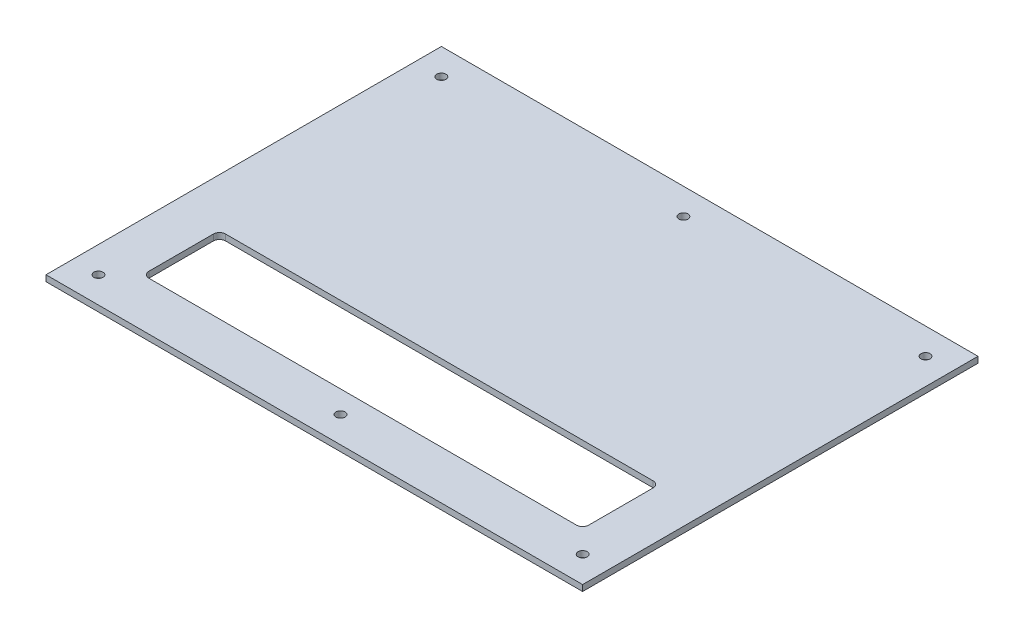
SolidWorks part; units mm, degrees
ref_plane "Спереди" through (0, 0, 0) normal (0, 0, 1) x (1, 0, 0)
ref_plane "Сверху" through (0, 0, 0) normal (0, 1, 0) x (1, 0, 0)
ref_plane "Справа" through (0, 0, 0) normal (1, 0, 0) x (0, 0, -1)
sketch "Эскиз1" plane through (0, 0, 0) normal (0, 1, 0) x (1, 0, 0)
  line L0 (0, 0) -> (266, 0)
  line L1 (0, 0) -> (0, 196)
  line L2 (266, 0) -> (266, 196)
  line L3 (0, 196) -> (266, 196)
  line L4 (13, 183) -> (253, 183) construction
  line L5 (13, 183) -> (13, 13) construction
  line L6 (253, 183) -> (253, 13) construction
  line L7 (13, 13) -> (253, 13) construction
  circle A0 centre (13, 183) radius 2.25
  circle A1 centre (253, 183) radius 2.25
  circle A2 centre (253, 13) radius 2.25
  circle A3 centre (13, 13) radius 2.25
  circle A4 centre (133, 13) radius 2.25
  circle A5 centre (133, 183) radius 2.25
  dimension "D7" = 4.5
  dimension "D8" = 4.5
  dimension "D9" = 4.5
  dimension "D10" = 4.5
  dimension "D11" = 4.5
  dimension "D12" = 4.5
  dimension "D1" = 196
  dimension "D2" = 266
  dimension "D3" = 13
  dimension "D4" = 13
  dimension "D5" = 13
  dimension "D6" = 13
extrude "Бобышка-Вытянуть1" add sketch "Эскиз1" along normal blind 3
sketch "Эскиз2" plane through (0, 3, 0) normal (0, 1, 0) x (1, 0, 0)
  line L0 (3, 193) -> (3, 3) construction
  line L1 (3, 193) -> (263, 193) construction
  line L2 (3, 3) -> (263, 3) construction
  line L3 (263, 193) -> (263, 3) construction
  line L4 (266, 196) -> (0, 196) construction
  line L5 (0, 196) -> (0, 0) construction
  dimension "D1" = 260
  dimension "D2" = 190
  dimension "D3" = 3
  dimension "D4" = 3
sketch "Sketch1" plane through (0, 0, 0) normal (0, -1, 0) x (1, 0, 0)
  line L0 (24, -24) -> (242, -24)
  line L1 (24, -24) -> (24, -62)
  line L2 (242, -24) -> (242, -62)
  line L3 (24, -62) -> (242, -62)
  line L4 (23, -43) -> (23, -62)
  line L5 (243, -43) -> (23, -43)
  line L6 (243, -62) -> (243, -43)
  line L7 (23, -62) -> (243, -62)
  line L8 (23, -43) -> (23, -62) construction
  line L9 (243, -43) -> (23, -43) construction
  line L10 (243, -62) -> (243, -43) construction
  line L11 (23, -62) -> (243, -62) construction
  line L12 (243, -43) -> (243, -23)
  line L13 (243, -23) -> (23, -23)
  line L14 (23, -23) -> (23, -43)
  line L15 (23, -43) -> (243, -43)
  line L16 (243, -43) -> (243, -23) construction
  line L17 (243, -23) -> (23, -23) construction
  line L18 (23, -23) -> (23, -43) construction
  line L19 (23, -43) -> (243, -43) construction
  dimension "D3" = 1
  dimension "D4" = 1
  dimension "D5" = 2
  dimension "D6" = 0
  dimension "D1" = 0
  dimension "D2" = 0
extrude "Cut-Extrude1" cut sketch "Sketch1" against normal through all
fillet "Fillet1" radius 3 4 edges at (242, 1.5, -62) (242, 1.5, -24) (24, 1.5, -62) (24, 1.5, -24)
